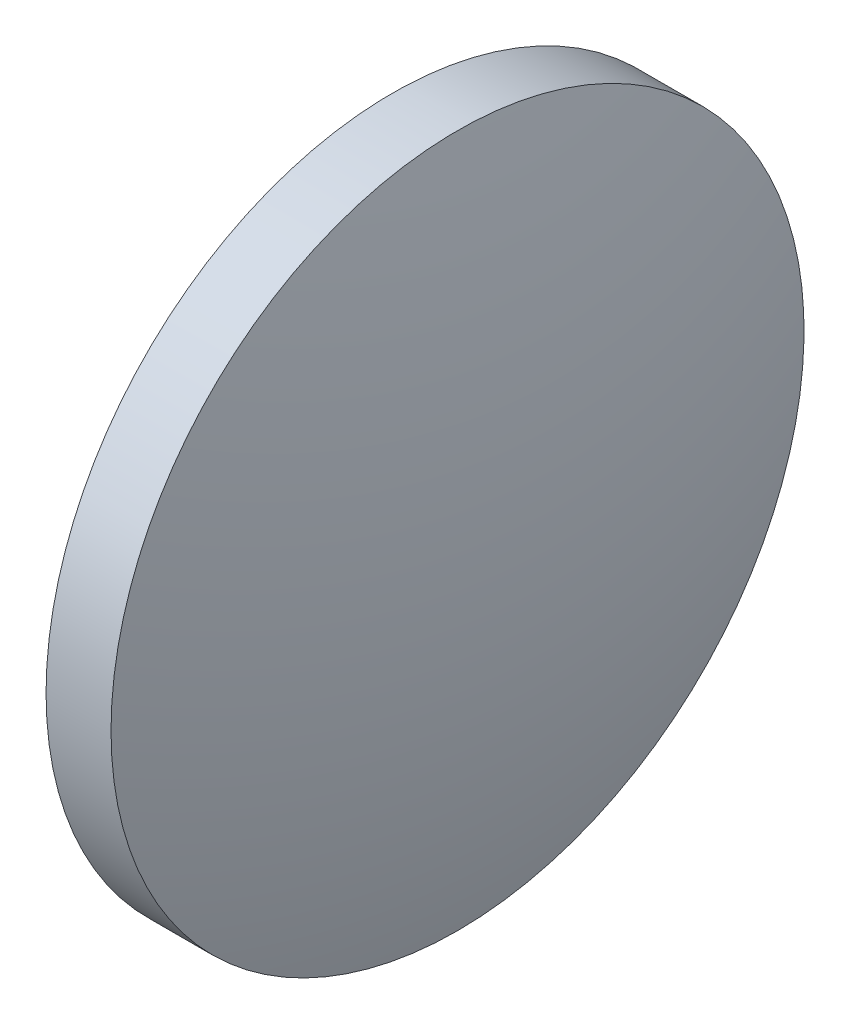
SolidWorks part; units mm, degrees
ref_plane "前视基准面" through (0, 0, 0) normal (0, 0, 1) x (1, 0, 0)
ref_plane "上视基准面" through (0, 0, 0) normal (0, 1, 0) x (1, 0, 0)
ref_plane "右视基准面" through (0, 0, 0) normal (1, 0, 0) x (0, 0, -1)
sketch "草图1" plane through (0, 0, 0) normal (0, 0, 1) x (1, 0, 0)
  line L0 (606.5455, 205.9704) -> (614.0639, 205.9704) construction
  line L1 (608.8265, 205.9704) -> (608.8265, 213.9704)
  line L2 (608.8265, 213.9704) -> (610.3265, 213.9704)
  line L3 (611.4565, 205.9704) -> (608.8265, 205.9704)
  arc A0 (611.4565, 205.9704) -> (610.3265, 213.9704) centre (582.5729, 205.9704) ccw
revolve "旋转1" add sketch "草图1" angle 360 about L0
